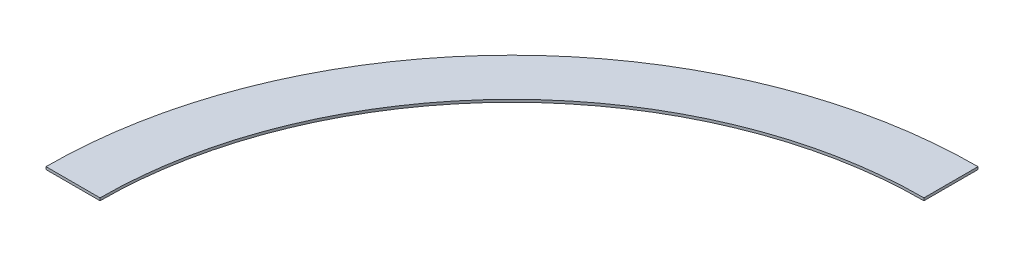
SolidWorks part; units mm, degrees
ref_plane "Ön Düzlem" through (0, 0, 0) normal (0, 0, 1) x (1, 0, 0)
ref_plane "Üst Düzlem" through (0, 0, 0) normal (0, 1, 0) x (1, 0, 0)
ref_plane "Sağ Düzlem" through (0, 0, 0) normal (1, 0, 0) x (0, 0, -1)
sketch "Çizim1" plane through (0, 0, 0) normal (0, 1, 0) x (1, 0, 0)
  line L0 (0, 181) -> (0, 160)
  line L1 (-160, 0) -> (-181, 0)
  circle A0 centre (0, 0) radius 160
  circle A1 centre (0, 0) radius 181
  dimension "D1" = 320
  dimension "D2" = 362
extrude "Yükseklik-Ekstrüzyon1" add sketch "Çizim1" along normal blind 1 contours L0 A1 L1 A0
